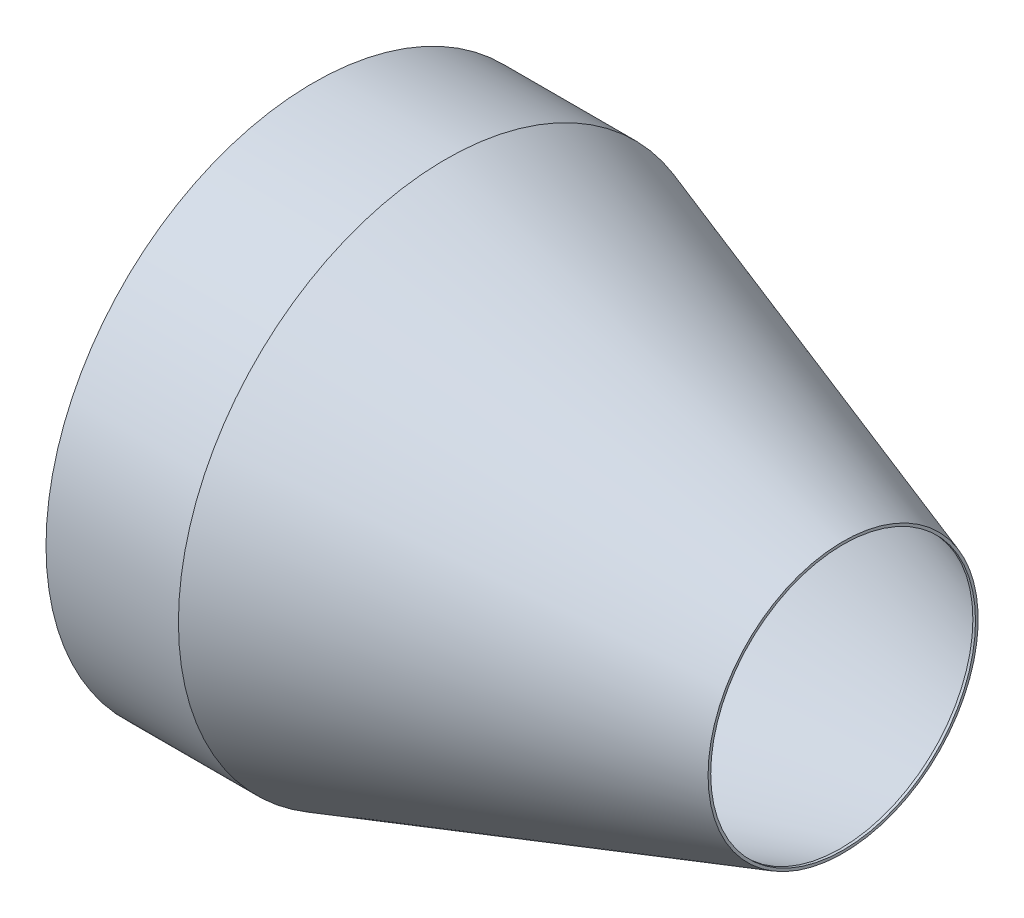
SolidWorks part; units mm, degrees
material "Gray Cast Iron"
ref_plane "Front Plane" through (0, 0, 0) normal (0, 0, 1) x (1, 0, 0)
ref_plane "Top Plane" through (0, 0, 0) normal (0, 1, 0) x (1, 0, 0)
ref_plane "Right Plane" through (0, 0, 0) normal (1, 0, 0) x (0, 0, -1)
sketch "Sketch1" plane through (0, 0, 0) normal (0, 0, 1) x (1, 0, 0)
  line L9 (0, 0) -> (50, 0)
  line L11 (0, 0) -> (0, 101)
  line L13 (0, 101) -> (200, 101)
  line L15 (200, 101) -> (200, 50)
  line L17 (50, 0) -> (200, 50)
  line L18 (49.8377, 1) -> (199, 50.7208)
  line L19 (199, 100) -> (199, 50.7208)
  line L20 (1, 100) -> (199, 100)
  line L21 (1, 1) -> (1, 100)
  line L22 (1, 1) -> (49.8377, 1)
revolve "Revolve1" add sketch "Sketch1" angle 360 about L13
sketch "Sketch2" plane through (200, 0, 0) normal (1, 0, 0) x (0, 0, -1)
  circle A0 centre (0, 101) radius 50
extrude "Cut-Extrude1" cut sketch "Sketch2" against normal blind 10
sketch "Sketch3" plane through (190, 0, 0) normal (1, 0, 0) x (0, 0, -1)
  circle A2 centre (0, 101) radius 1
extrude "Cut-Extrude2" cut sketch "Sketch3" against normal blind 180 contours A2
sketch "Sketch4" plane through (10, 0, 0) normal (1, 0, 0) x (0, 0, -1)
  circle A0 centre (0, 101) radius 1
extrude "Cut-Extrude3" cut sketch "Sketch4" against normal blind 1
sketch "Sketch5" plane through (0, 0, 0) normal (-1, 0, 0) x (0, 0, 1)
  circle A1 centre (0, 101) radius 99.5
  dimension "D1" = 199
extrude "Cut-Extrude7" cut sketch "Sketch5" against normal blind 26
